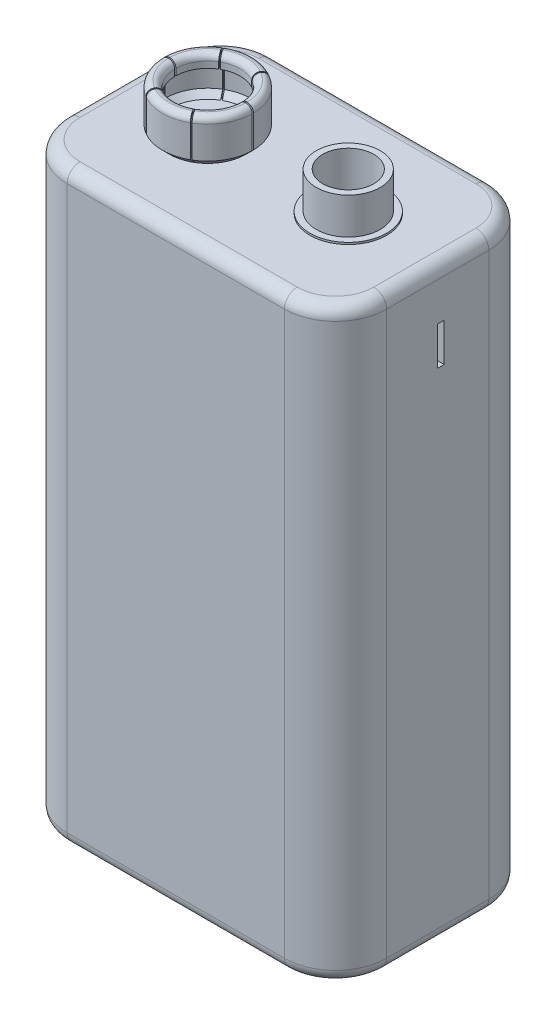
SolidWorks part; units mm, degrees
ref_plane "Front Plane" through (0, 0, 0) normal (0, 0, 1) x (1, 0, 0)
ref_plane "Top Plane" through (0, 0, 0) normal (0, 1, 0) x (1, 0, 0)
ref_plane "Right Plane" through (0, 0, 0) normal (1, 0, 0) x (0, 0, -1)
sketch "Sketch2" plane through (0, 0, 0) normal (0, 1, 0) x (1, 0, 0)
  line L1 (-12.5, -8) -> (12.5, -8)
  line L2 (-12.5, -8) -> (-12.5, 8)
  line L3 (-12.5, 8) -> (12.5, 8)
  line L4 (12.5, -8) -> (12.5, 8)
  line L5 (-12.5, -8) -> (12.5, 8) construction
  line L6 (-12.5, 8) -> (12.5, -8) construction
  point P0 (0, 0)
  dimension "D1" = 25
  dimension "D2" = 16
extrude "Boss-Extrude1" add sketch "Sketch2" along normal blind 46
fillet "Fillet1" radius 4 4 edges at (-12.5, 23, -8) (-12.5, 23, 8) (12.5, 23, -8) (12.5, 23, 8)
fillet "Fillet2" radius 1 16 edges at (-11.3284, 0, 6.8284) (0, 0, 8) (11.3284, 0, 6.8284) (12.5, 0, 0) (11.3284, 0, -6.8284) (0, 0, -8) (-11.3284, 0, -6.8284) (-12.5, 0, 0) (11.3284, 46, -6.8284) (12.5, 46, 0) (11.3284, 46, 6.8284) (0, 46, 8) (-11.3284, 46, 6.8284) (-12.5, 46, 0) (-11.3284, 46, -6.8284) (0, 46, -8)
sketch "Sketch3" plane through (0, 46, 0) normal (0, 1, 0) x (1, 0, 0)
  circle A0 centre (5.5, 0) radius 2.5
  dimension "D1" = 5
  dimension "D2" = 5.5
sketch "Sketch6" plane through (0, 46, 0) normal (0, 1, 0) x (1, 0, 0)
  circle A0 centre (-5.5, 0) radius 1
  circle A1 centre (5.5, 0) radius 1
  dimension "D1" = 2
  dimension "D2" = 2
  dimension "D3" = 11
  dimension "D4" = 5.5
extrude "Extrude-Thin1" add sketch "Sketch3" along normal blind 3 thin thin type one direction reverse wall 0.5
extrude "Boss-Extrude2" add sketch "Sketch6" along normal blind 0.75
ref_axis "Axis1" through (-5.5, 46.75, 0) along (0, -1, 0)
sketch "Sketch9" plane through (0, 0, 0) normal (0, 0, 1) x (1, 0, 0)
  line L0 (-4.5, 46) -> (-2.5, 46)
  line L2 (-2.5, 46) -> (-1.9697, 46.5303)
  line L3 (-1.9697, 46.5303) -> (-1.9697, 49.0303)
  line L5 (-2.9642, 49.0303) -> (-2.9642, 48.5352)
  arc A0 (-2.4691, 49.5255) -> (-2.9642, 49.0303) centre (-2.4691, 49.0303) ccw
  arc A1 (-1.9697, 49.0303) -> (-2.4691, 49.5255) centre (-2.4648, 49.0303) ccw
  dimension "D1" = 2
  dimension "D2" = 2.5
  dimension "D3" = 0.75
revolve "Revolve-Thin1" add sketch "Sketch9" angle 360 about axis through (-5.5, 46.75, 0) along (0, -1, 0) wall 0.15
sketch "Sketch10" plane through (0, 46.15, 0) normal (0, 1, 0) x (1, 0, 0)
  line L1 (-3.2191, -0.05) -> (-1.7191, -0.05)
  line L2 (-3.2191, -0.05) -> (-3.2191, 0.05)
  line L3 (-3.2191, 0.05) -> (-1.7191, 0.05)
  line L4 (-1.7191, -0.05) -> (-1.7191, 0.05)
  line L5 (-3.2191, -0.05) -> (-1.7191, 0.05) construction
  line L6 (-3.2191, 0.05) -> (-1.7191, -0.05) construction
  circle A0 centre (-5.5, 0) radius 3.0309 construction
  point P0 (-2.4691, 0)
  dimension "D1" = 0.1
  dimension "D2" = 1.5
extrude "Cut-Extrude1" cut sketch "Sketch10" along normal through all
pattern_circular "CirPattern1" count 6 over 360 about axis through (-5.5, 0, 0) along (0, 1, 0) of "Cut-Extrude1"
sketch "Sketch11" plane through (0, 46, 0) normal (0, 1, 0) x (1, 0, 0)
  circle A0 centre (5.5, 0) radius 3
  dimension "D1" = 6
extrude "Boss-Extrude3" add sketch "Sketch11" along normal blind 0.15
sketch "Sketch12" plane through (-12.5, 0, 0) normal (-1, 0, 0) x (0, 0, 1)
  line L0 (-0.5, 40) -> (-2, 40)
  line L1 (-2, 40) -> (-2, 40.5)
  line L2 (-2, 40.5) -> (-0.5, 40.5)
  line L3 (-0.5, 40.5) -> (-0.5, 42)
  line L4 (-0.5, 42) -> (0, 42)
  line L5 (0, 42) -> (0, 40.5)
  line L6 (0, 40.5) -> (1.5, 40.5)
  line L7 (1.5, 40.5) -> (1.5, 40)
  line L8 (1.5, 40) -> (0, 40)
  line L9 (0, 40) -> (0, 38.5)
  line L10 (0, 38.5) -> (-0.5, 38.5)
  line L11 (-0.5, 38.5) -> (-0.5, 40)
  line L12 (-0.5, 40) -> (-0.5365, 40.0387)
  line L14 (4, 45) -> (-4, 45) construction
  dimension "D1" = 0.5
  dimension "D2" = 1.5
  dimension "D3" = 1.5
  dimension "D4" = 0.5
  dimension "D5" = 1.5
  dimension "D6" = 1.5
  dimension "D7" = 1.5
  dimension "D8" = 0.5
  dimension "D9" = 3
extrude "Cut-Extrude2" cut sketch "Sketch12" against normal blind 1
sketch "Sketch13" plane through (12.5, 0, 0) normal (1, 0, 0) x (0, 0, -1)
  line L0 (4, 45) -> (-4, 45) construction
  line L1 (0.5, 42) -> (0, 42)
  line L2 (0.5, 42) -> (0.5, 39)
  line L3 (0.5, 39) -> (0, 39)
  line L4 (0, 42) -> (0, 39)
  point P4 (0.25, 42)
  point P7 (0, 45)
  dimension "D1" = 3
  dimension "D2" = 0.5
  dimension "D3" = 3
extrude "Cut-Extrude3" cut sketch "Sketch13" against normal blind 1
